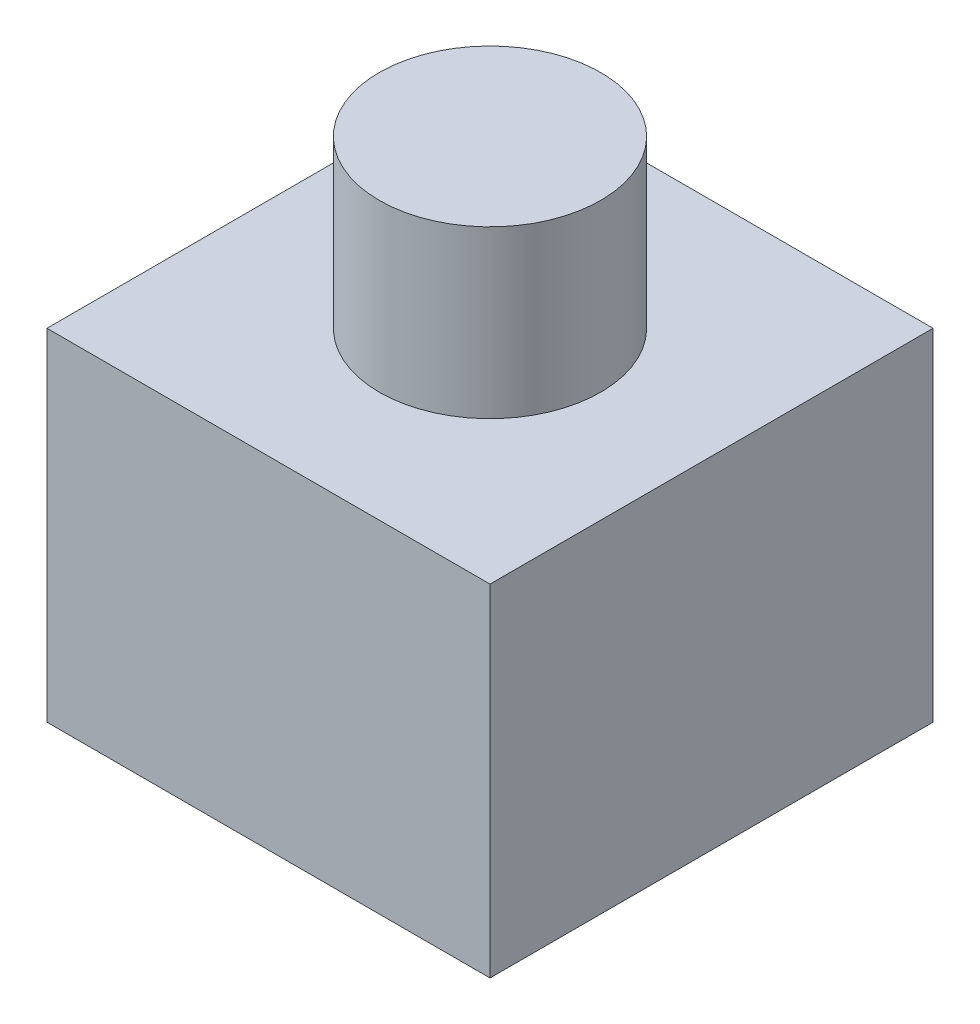
SolidWorks part; units mm, degrees
ref_plane "Front Plane" through (0, 0, 0) normal (0, 0, 1) x (1, 0, 0)
ref_plane "Top Plane" through (0, 0, 0) normal (0, 1, 0) x (1, 0, 0)
ref_plane "Right Plane" through (0, 0, 0) normal (1, 0, 0) x (0, 0, -1)
sketch "Sketch1" plane through (0, 0, 0) normal (0, 1, 0) x (1, 0, 0)
  line L1 (0, 0) -> (25.4, 0)
  line L2 (0, 0) -> (0, 25.4)
  line L3 (0, 25.4) -> (25.4, 25.4)
  line L4 (25.4, 0) -> (25.4, 25.4)
  dimension "D1" = 25.4
  dimension "D2" = 25.4
extrude "Boss-Extrude1" add sketch "Sketch1" along normal blind 19.558
sketch "Sketch2" plane through (0, 19.558, 0) normal (0, 1, 0) x (1, 0, 0)
  line L0 (12.7, 25.4) -> (12.7, 0) construction
  line L1 (25.4, 25.4) -> (0, 25.4) construction
  line L2 (0, 0) -> (25.4, 0) construction
  circle A0 centre (12.7, 12.7) radius 6.35
  point P8 (15.875, 12.7)
  dimension "D1" = 12.7
extrude "Boss-Extrude2" add sketch "Sketch2" along normal blind 9.525
